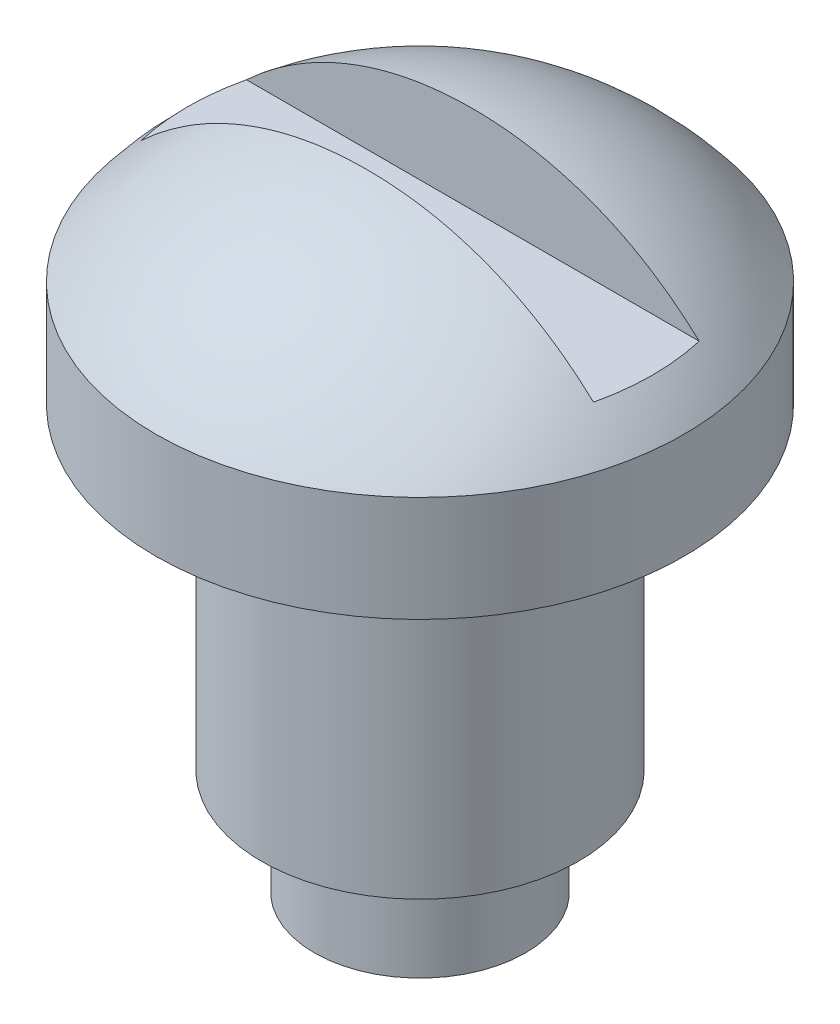
SolidWorks part; units mm, degrees
ref_plane "Ön Düzlem" through (0, 0, 0) normal (0, 0, 1) x (1, 0, 0)
ref_plane "Üst Düzlem" through (0, 0, 0) normal (0, 1, 0) x (1, 0, 0)
ref_plane "Sağ Düzlem" through (0, 0, 0) normal (1, 0, 0) x (0, 0, -1)
sketch "Çizim2" plane through (0, 0, 0) normal (0, 0, 1) x (1, 0, 0)
  line L7 (0, 0) -> (0, 24.7874) construction
  line L8 (0, 0) -> (2, 0)
  line L10 (2, 0) -> (2, 2)
  line L11 (2, 2) -> (3, 2)
  line L12 (3, 2) -> (3, 8)
  line L13 (3, 8) -> (5, 8)
  line L14 (5, 8) -> (5, 10)
  line L15 (0, 12.4) -> (0, 0)
  arc A8 (5, 10) -> (0, 12.4) centre (0.1004, 6.2008) ccw
  point P12 (2, 1)
  dimension "D1" = 4
  dimension "D7" = 6.2
  dimension "D2" = 2
  dimension "D8" = 10
  dimension "D3" = 6
  dimension "D4" = 6
  dimension "D5" = 2
  dimension "D6" = 12.4
revolve "Döndür3" add sketch "Çizim2" angle 360 about L7
sketch "Çizim9" plane through (0, 0, 0) normal (1, 0, 0) x (0, 0, -1)
  line L0 (0, 12.4) -> (0, 10.6683) construction
  line L1 (0, 10.6683) -> (-1, 10.6683) construction
  line L2 (0, 10.6683) -> (1, 10.6683) construction
  line L4 (1, 10.6683) -> (-1, 10.6683)
  line L5 (1, 10.6683) -> (1, 12.4008)
  line L6 (1, 12.4008) -> (-1, 12.4008)
  line L7 (-1, 10.6683) -> (-1, 12.4008)
  dimension "D1" = 1
  dimension "D2" = 1
extrude "Kes-Ekstrüzyon12" cut sketch "Çizim9" against normal up to surface (4.2843 mm away)
mirror "Aynalama2" about plane through (0, 0, 0) normal (1, 0, 0) of "Kes-Ekstrüzyon12"
